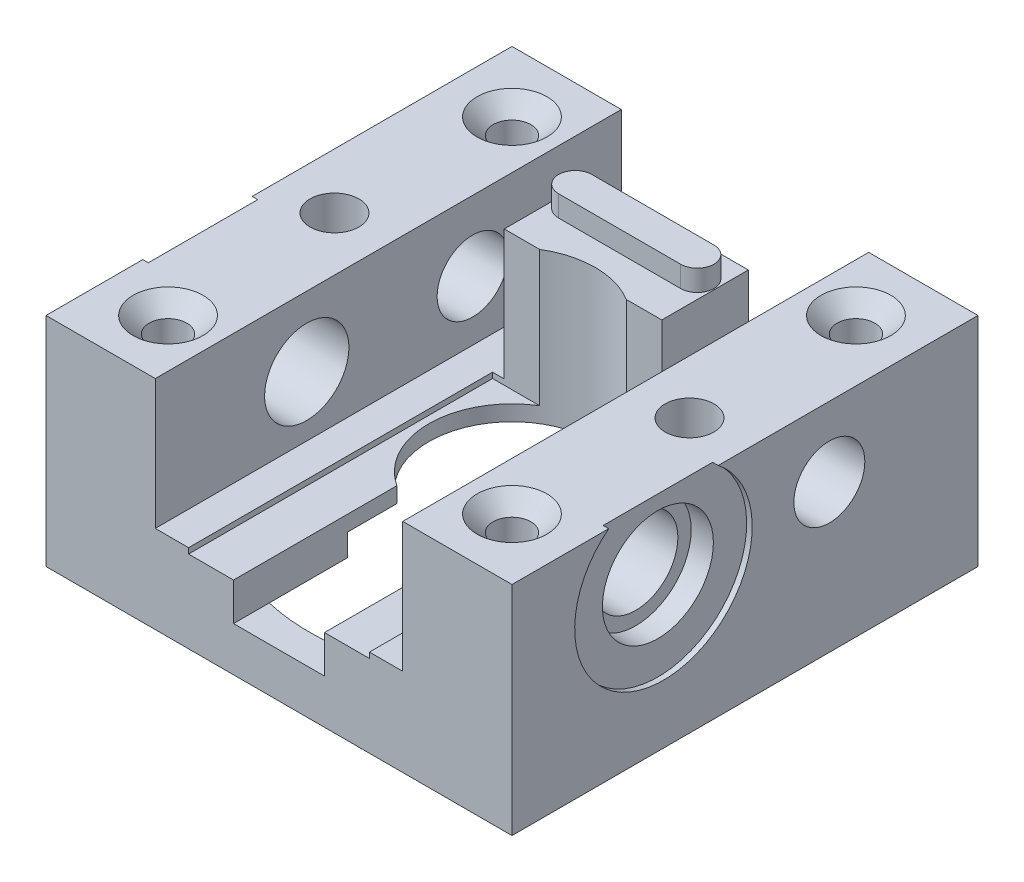
SolidWorks part; units mm, degrees
ref_plane "Alzado" through (0, 0, 0) normal (0, 0, 1) x (1, 0, 0)
ref_plane "Planta" through (0, 0, 0) normal (0, 1, 0) x (1, 0, 0)
ref_plane "Vista lateral" through (0, 0, 0) normal (1, 0, 0) x (0, 0, -1)
sketch "Croquis3" plane through (0, 0, 0) normal (0, 1, 0) x (1, 0, 0)
  line L1 (-21, 21) -> (21, 21)
  line L2 (-21, 21) -> (-21, -21)
  line L3 (-21, -21) -> (21, -21)
  line L4 (21, 21) -> (21, -21)
  line L5 (-21, 21) -> (21, -21) construction
  line L6 (-21, -21) -> (21, 21) construction
  point P0 (0, 0)
  dimension "D1" = 42
  dimension "D2" = 42
extrude "Saliente-Extruir1" add sketch "Croquis3" against normal blind 19.6
sketch "Croquis4" plane through (0, 0, 0) normal (0, 1, 0) x (1, 0, 0)
  line L0 (0, 21) -> (0, -21) construction
  line L1 (21, 21) -> (-21, 21) construction
  line L2 (-21, -21) -> (21, -21) construction
  line L3 (-11.15, 21) -> (-11.15, -21)
  line L4 (11.15, 21) -> (11.15, -21)
  line L5 (-11.15, 21) -> (11.15, 21)
  line L6 (-11.15, -21) -> (11.15, -21)
  line L7 (-7.1, 14.2) -> (7.1, 14.2)
  line L8 (-7.1, 14.2) -> (-7.1, 6.4)
  line L9 (7.1, 14.2) -> (7.1, 6.4)
  line L10 (-7.1, 6.4) -> (7.1, 6.4)
  line L12 (-7.1, 21) -> (-7.1, -21) construction
  line L13 (7.1, 21) -> (7.1, -21) construction
  line L14 (-11.15, 14.2) -> (11.15, 14.2) construction
  line L15 (-11.15, 6.4) -> (11.15, 6.4) construction
  dimension "D1" = 11.15
  dimension "D2" = 11.15
  dimension "D3" = 6.8
  dimension "D4" = 7.1
  dimension "D5" = 7.1
  dimension "D6" = 7.8
extrude "Cortar-Extruir1" cut sketch "Croquis4" against normal blind 11.7
sketch "Croquis5" plane through (0, -11.7, 0) normal (0, 1, 0) x (1, 0, 0)
  line L4 (-8.15, 21) -> (-8.15, 14.2)
  line L5 (8.15, -21) -> (8.15, 6.4)
  line L6 (-7.1, 6.4) -> (7.1, 6.4) construction
  line L7 (-8.15, 6.4) -> (8.15, 6.4)
  line L8 (7.1, 14.2) -> (-7.1, 14.2) construction
  line L9 (8.15, 14.2) -> (-8.15, 14.2)
  line L10 (-8.15, 6.4) -> (-8.15, -21)
  line L11 (8.15, 14.2) -> (8.15, 21)
  line L13 (-8.15, 21) -> (8.15, 21)
  line L15 (-8.15, -21) -> (8.15, -21)
extrude "Cortar-Extruir2" cut sketch "Croquis5" against normal blind 0.5
sketch "Croquis6" plane through (0, -12.2, 0) normal (0, 1, 0) x (1, 0, 0)
  line L0 (0, -21) -> (0, 21) construction
  line L1 (-8.15, -21) -> (8.15, -21) construction
  line L2 (8.15, 21) -> (-8.15, 21) construction
  line L3 (4.1, -21) -> (4.1, -6.2801)
  line L4 (-4.1, -21) -> (-4.1, -6.2801)
  line L7 (-4.1, -21) -> (-4.1, 21) construction
  line L8 (-4.1, -21) -> (4.1, -21)
  line L9 (4.1, -21) -> (4.1, 21) construction
  arc A0 (4.1, -6.2801) -> (-4.1, -6.2801) centre (0, 0) ccw
  dimension "D3" = 15
  dimension "D1" = 4.1
  dimension "D2" = 4.1
extrude "Cortar-Extruir3" cut sketch "Croquis6" against normal blind 3.4 and the other way up to surface contours A0 L4 L8 L3
sketch "Croquis7" plane through (0, -19.6, 0) normal (0, -1, 0) x (1, 0, 0)
  circle A0 centre (0, 0) radius 18.25
  dimension "D1" = 36.5
extrude "Cortar-Extruir4" cut sketch "Croquis7" against normal blind 4
sketch "Croquis8" plane through (0, -15.6, 0) normal (0, -1, 0) x (1, 0, 0)
  circle A0 centre (0, 0) radius 11.5
  dimension "D1" = 23
extrude "Cortar-Extruir5" cut sketch "Croquis8" against normal blind 2
sketch "Croquis9" plane through (0, -15.6, 0) normal (0, -1, 0) x (1, 0, 0)
  line L0 (-21, 0) -> (21, 0) construction
  line L1 (-21, -21) -> (-21, 21) construction
  line L2 (21, 21) -> (21, -21) construction
  line L3 (0, 21) -> (0, -21) construction
  line L4 (-21, 21) -> (21, 21) construction
  line L5 (21, -21) -> (-21, -21) construction
  line L6 (-16, 21) -> (-16, -21) construction
  line L7 (16, 21) -> (16, -21) construction
  circle A0 centre (-16, 0) radius 2.2
  circle A1 centre (16, 0) radius 2.2
  dimension "D3" = 4.4
  dimension "D4" = 4.4
  dimension "D1" = 16
  dimension "D2" = 16
extrude "Cortar-Extruir6" cut sketch "Croquis9" against normal up to surface (15.6 mm away) up to face at (-16.075, 0, 0)
hole_wizard "Avellanado para tornillo con cabeza plana avellanada de M31" positions "Croquis11" profile "Croquis10" countersink size "M3" standard "ISO" end condition through all
sketch "Croquis11" plane through (0, 0, 0) normal (0, 1, 0) x (1, 0, 0)
  line L0 (-11.15, 21) -> (-21, 21) construction
  line L2 (-21, 21) -> (-21, -21) construction
  point P0 (-15.5, 15.5)
  point P2 (15.5, 15.5)
  point P4 (15.5, -15.5)
  point P6 (-15.5, -15.5)
  dimension "D1" = 31
  dimension "D2" = 31
  dimension "D3" = 5.5
  dimension "D4" = 5.5
sketch "Croquis10" plane through (-15.5, 0, -15.5) normal (1, 0, 0) x (0, 0, 1)
  line L0 (0, 0) -> (0, 19.6)
  line L1 (0, 19.6) -> (1.7, 19.6)
  line L2 (1.7, 19.6) -> (1.7, 1.45)
  line L3 (1.7, 1.45) -> (3.15, 0)
  line L5 (3.15, 0) -> (0, 0)
  line L6 (-1.7, 1.45) -> (-3.15, 0) construction
  line L11 (0, -6.35) -> (0, 107.95) construction
  dimension "Diámetro de taladro hasta el siguiente" = 3.4
  dimension "Profundidad de taladro hasta el siguiente" = 19.6
  dimension "Diámetro de avellanado cercano" = 6.3
  dimension "Ángulo de avellanado cercano" = 90
sketch "Croquis12" plane through (0, 0, 0) normal (0, 1, 0) x (1, 0, 0)
  line L1 (0, 14.2) -> (0, 7.5) construction
  line L2 (7.1, 11.2) -> (-7.1, 11.2) construction
  line L3 (7.1, 14.2) -> (-7.1, 14.2) construction
  line L4 (-5.5, 11.2) -> (5.5, 11.2) construction
  line L5 (-5.5, 12.7) -> (5.5, 12.7)
  line L6 (-5.5, 9.7) -> (5.5, 9.7)
  arc A0 (3.9102, 6.4) -> (-3.9102, 6.4) centre (0, 0) ccw construction
  arc A1 (-5.5, 12.7) -> (-5.5, 9.7) centre (-5.5, 11.2) ccw
  arc A2 (5.5, 9.7) -> (5.5, 12.7) centre (5.5, 11.2) ccw
  point P11 (0, 11.2)
  dimension "D1" = 3
extrude "Saliente-Extruir3" add sketch "Croquis12" along normal blind 1.9
sketch "Croquis13" plane through (21, 0, 0) normal (1, 0, 0) x (0, 0, -1)
  line L2 (-7.35, -19.6) -> (-7.35, 0)
  line L3 (-7.35, -19.6) -> (-7.35, 0) construction
  line L5 (-21, -6.3) -> (21, -6.3)
  line L6 (-21, -6.3) -> (21, -6.3) construction
  circle A0 centre (-7.35, -6.3) radius 8
  dimension "D3" = 16
  dimension "D1" = 13.65
  dimension "D2" = 6.3
extrude "Cortar-Extruir7" cut sketch "Croquis13" against normal blind 0.5
sketch "Croquis14" plane through (20.5, 0, 0) normal (1, 0, 0) x (0, 0, -1)
  line L0 (-7.35, -14.3) -> (-7.35, 0) construction
  line L1 (-12.2805, 0) -> (-2.4195, 0) construction
  line L2 (-15.35, -6.3) -> (0.65, -6.3) construction
  arc A0 (-12.2805, 0) -> (-2.4195, 0) centre (-7.35, -6.3) ccw construction
  arc A1 (-12.2805, 0) -> (-2.4195, 0) centre (-7.35, -6.3) ccw construction
  circle A2 centre (-7.35, -6.3) radius 5
extrude "Cortar-Extruir8" cut sketch "Croquis14" against normal blind 2
hole_wizard "Diámetro de taladro Ø7.6 (7.6)1" positions "Croquis16" profile "Croquis15" hole size "Ø7.6" standard "ISO" end condition through all
sketch "Croquis16" plane through (18.5, 0, 0) normal (1, 0, 0) x (0, 0, -1)
  point P0 (-7.35, -6.3)
sketch "Croquis15" plane through (18.5, -6.3, 7.35) normal (0, 1, 0) x (0, 0, -1)
  line L0 (0, 0) -> (0, 39.5)
  line L1 (0, 39.5) -> (3.8, 39.5)
  line L2 (3.8, 39.5) -> (3.8, 0)
  line L5 (3.8, 0) -> (0, 0)
  line L11 (0, -6.35) -> (0, 107.95) construction
  dimension "Diámetro de taladro hasta el siguiente" = 7.6
  dimension "Profundidad de taladro hasta el siguiente" = 39.5
sketch "Croquis17" plane through (-21, 0, 0) normal (-1, 0, 0) x (0, 0, 1)
  circle A0 centre (7.35, -6.3) radius 8
extrude "Cortar-Extruir9" cut sketch "Croquis17" against normal blind 0.5
sketch "Croquis18" plane through (-20.5, 0, 0) normal (-1, 0, 0) x (0, 0, 1)
  circle A0 centre (7.35, -6.3) radius 5
extrude "Cortar-Extruir10" cut sketch "Croquis18" against normal blind 2
sketch "Croquis19" plane through (0, 0, -14.2) normal (0, 0, -1) x (-1, 0, 0)
  line L10 (-7.1, -6.2) -> (7.1, -6.2)
  line L11 (-7.1, -6.2) -> (7.1, -6.2) construction
  line L13 (-4, -11.7) -> (-4, 0)
  line L14 (-4, -11.7) -> (-4, 0) construction
  line L16 (4, -11.7) -> (4, 0)
  line L17 (4, -11.7) -> (4, 0) construction
  circle A0 centre (4, -6.2) radius 2.7
  circle A1 centre (-4, -6.2) radius 2.7
  dimension "D4" = 8
  dimension "D1" = 6.2
  dimension "D2" = 3.1
  dimension "D3" = 3.1
extrude "Cortar-Extruir11" cut sketch "Croquis19" against normal blind 4.9
sketch "Croquis20" plane through (-21, 0, 0) normal (-1, 0, 0) x (0, 0, 1)
  line L0 (3.55, -6.3) -> (-24.8673, -6.3) construction
  line L3 (-7.6, -19.6) -> (-7.6, 0)
  line L4 (-7.6, -19.6) -> (-7.6, 0) construction
  circle A0 centre (7.35, -6.3) radius 3.8 construction
  dimension "D1" = 13.4
hole_wizard "Diámetro de taladro Ø6.4 (6.4)1" positions "Croquis22" profile "Croquis21" hole size "Ø6.4" standard "ISO" end condition up to next
sketch "Croquis22" plane through (-21, 0, 0) normal (-1, 0, 0) x (0, 0, 1)
  line L0 (3.55, -6.3) -> (-24.8673, -6.3) construction
  line L1 (-7.6, -19.6) -> (-7.6, 0) construction
  point P0 (-7.6, -6.3)
sketch "Croquis21" plane through (-21, -6.3, -7.6) normal (0, 1, 0) x (0, 0, 1)
  line L0 (0, 0) -> (0, 9.85)
  line L1 (0, 9.85) -> (3.2, 9.85)
  line L2 (3.2, 9.85) -> (3.2, 0)
  line L5 (3.2, 0) -> (0, 0)
  line L11 (0, -6.35) -> (0, 107.95) construction
  dimension "Diámetro de taladro hasta el siguiente" = 6.4
  dimension "Profundidad de taladro hasta el siguiente" = 9.85
hole_wizard "Diámetro de taladro Ø6.4 (6.4)2" positions "Croquis24" profile "Croquis23" hole size "Ø6.4" standard "ISO" end condition up to next
sketch "Croquis24" plane through (21, 0, 0) normal (1, 0, 0) x (0, 0, -1)
  line L0 (-3.55, -6.3) -> (24.8673, -6.3) construction
  line L1 (7.6, -19.6) -> (7.6, 0) construction
  point P2 (7.6, -6.3)
sketch "Croquis23" plane through (21, -6.3, -7.6) normal (0, 1, 0) x (0, 0, -1)
  line L0 (0, 0) -> (0, 9.85)
  line L1 (0, 9.85) -> (3.2, 9.85)
  line L2 (3.2, 9.85) -> (3.2, 0)
  line L5 (3.2, 0) -> (0, 0)
  line L11 (0, -6.35) -> (0, 107.95) construction
  dimension "Diámetro de taladro hasta el siguiente" = 6.4
  dimension "Profundidad de taladro hasta el siguiente" = 9.85
equation "\"D4@Croquis9\"=\"D3@Croquis9\""
